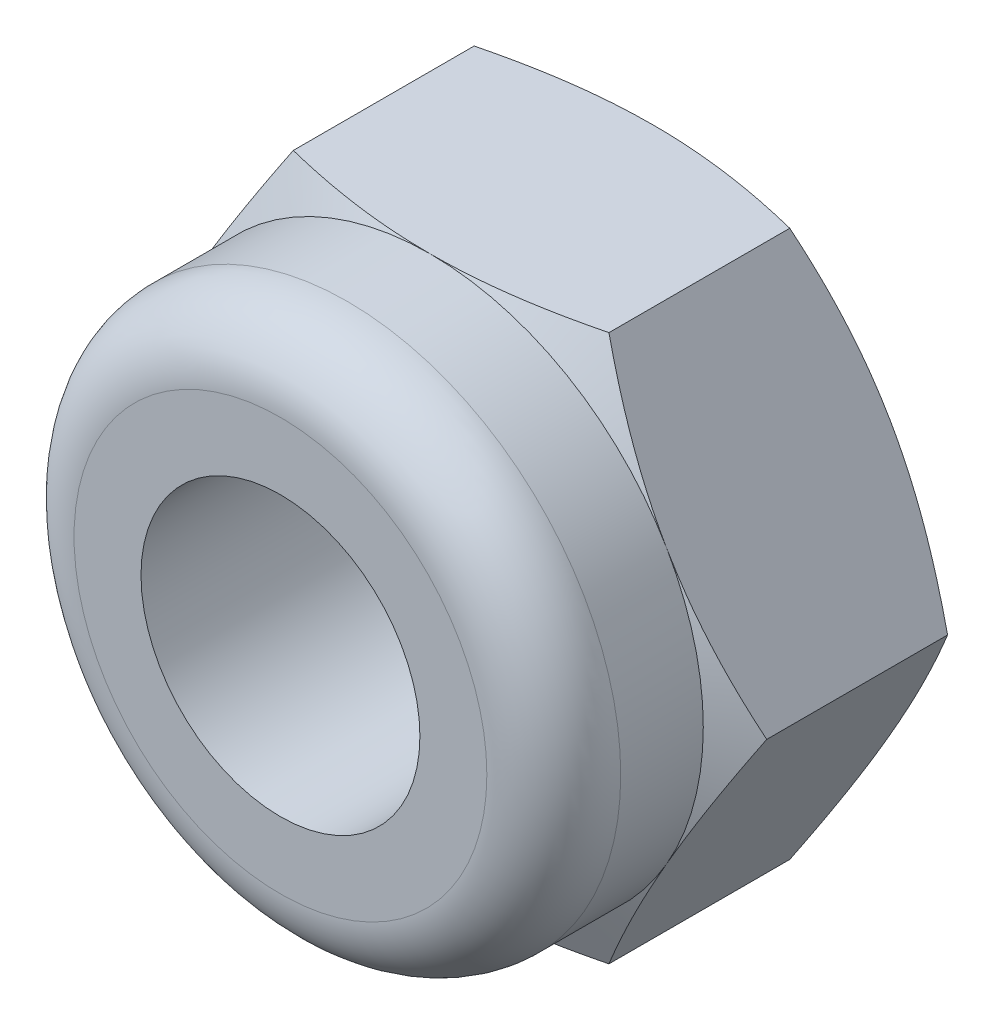
SolidWorks part; units mm, degrees
ref_plane "Front Plane" through (0, 0, 0) normal (0, 0, 1) x (1, 0, 0)
ref_plane "Top Plane" through (0, 0, 0) normal (0, 1, 0) x (1, 0, 0)
ref_plane "Right Plane" through (0, 0, 0) normal (1, 0, 0) x (0, 0, -1)
sketch "Sketch1" plane through (0, 0, 0) normal (0, 0, 1) x (1, 0, 0)
  line L0 (0, 2.829) -> (0, 0) construction
  line L1 (0, 0) -> (2.829, 0) construction
  line L2 (-1.4145, 2.45) -> (1.4145, 2.45)
  line L3 (1.4145, 2.45) -> (2.829, 0)
  line L4 (1.4145, -2.45) -> (2.829, 0)
  line L5 (-1.4145, -2.45) -> (1.4145, -2.45)
  line L6 (-1.4145, 2.45) -> (-2.829, 0)
  line L7 (-1.4145, -2.45) -> (-2.829, 0)
  circle A0 centre (0, 0) radius 2.829 construction
  circle A1 centre (0, 0) radius 2.45 construction
  circle A2 centre (0, 0) radius 1.25
  point P12 (0, 2.45)
  point P14 (0, -2.45)
  dimension "D1" = 4.9
  dimension "D2" = 2.5
extrude "Boss-Extrude1" add sketch "Sketch1" along normal blind 2
sketch "Sketch2" plane through (0, 0, 2) normal (0, 0, 1) x (1, 0, 0)
  line L0 (-1.4145, 2.45) -> (-2.829, 0) construction
  circle A0 centre (0, 0) radius 2.45
  circle A1 centre (0, 0) radius 1.25 construction
  circle A2 centre (0, 0) radius 1.25
extrude "Boss-Extrude2" add sketch "Sketch2" along normal blind 1.34
fillet "Fillet1" radius 0.6 1 edges at (2.45, 0, 3.34)
sketch "Sketch3" plane through (0, 0, 0) normal (1, 0, 0) x (0, 0, -1)
  line L0 (-2, 2.45) -> (-1.75, 2.95)
  line L1 (-1.75, 2.95) -> (-0.25, 2.95)
  line L2 (-0.25, 2.95) -> (0, 2.45)
  line L3 (0, 2.45) -> (0, 3.3732)
  line L4 (0, 3.3732) -> (-2, 3.3732)
  line L5 (-2, 3.3732) -> (-2, 2.45)
  line L6 (-2, 2.45) -> (0, 2.45) construction
  line L8 (0, 0) -> (1.9305, 0) construction
  point P9 (-1, 3.3732)
  point P12 (-1.75, 2.95)
  point P14 (-1, 2.95)
  dimension "D1" = 0.5
revolve "Cut-Revolve1" cut sketch "Sketch3" angle 360 about L8
chamfer "Chamfer1" distance 0.3 angle 45 1 edges at (1.25, 0, 0)
